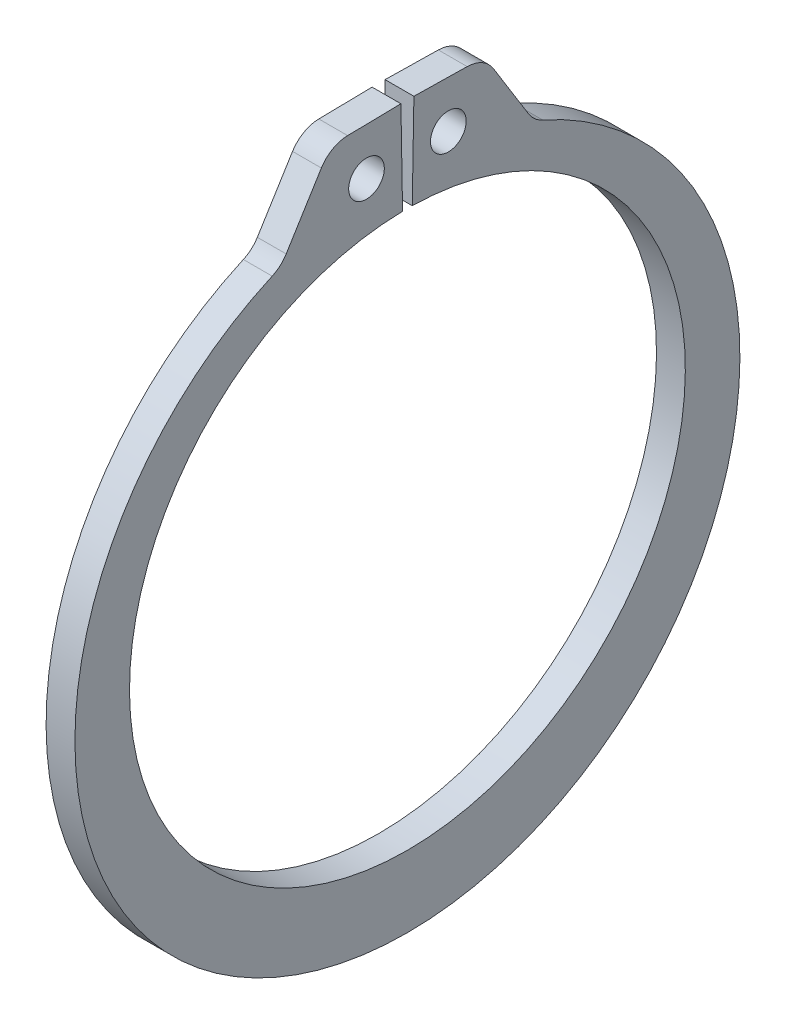
SolidWorks part; units mm, degrees
material "Cast Carbon Steel"
ref_plane "Front" through (0, 0, 0) normal (0, 0, 1) x (1, 0, 0)
ref_plane "Top" through (0, 0, 0) normal (0, 1, 0) x (1, 0, 0)
ref_plane "Right" through (0, 0, 0) normal (1, 0, 0) x (0, 0, -1)
sketch "Sketch1" plane through (0, 0, 0) normal (1, 0, 0) x (0, 0, -1)
  line L0 (0, 0) -> (0, 10.287) construction
  line L1 (-0.1795, 10.2854) -> (-0.2403, 13.7647)
  line L2 (0.2403, 13.7647) -> (2.8497, 13.7192)
  line L3 (2.8497, 13.7192) -> (4.6815, 10.7605)
  line L4 (0.1795, 10.2854) -> (0.2403, 13.7647)
  line L5 (-0.2403, 13.7647) -> (-2.8497, 13.7192)
  line L6 (-2.8497, 13.7192) -> (-4.6815, 10.7605)
  line L7 (-4.6815, 10.7605) -> (-4.1039, 9.4329) construction
  line L8 (4.6815, 10.7605) -> (4.1039, 9.4329) construction
  line L9 (0, -10.287) -> (0, -12.9286) construction
  line L10 (-2.8497, 13.7192) -> (-0.1795, 10.2854) construction
  line L11 (0, 10.287) -> (0, 13.7668) construction
  line L12 (-10.287, 0) -> (10.287, 0) construction
  circle A0 centre (0, 0) radius 10.287 construction
  arc A1 (-0.1795, 10.2854) -> (0.1795, 10.2854) centre (0, 0) ccw
  circle A3 centre (0, 0) radius 15.0495 construction
  circle A4 centre (-1.5146, 12.0023) radius 0.6604
  circle A5 centre (1.5146, 12.0023) radius 0.6604
  arc A6 (-4.6815, 10.7605) -> (4.6815, 10.7605) centre (0, -0.6214) ccw
  point P0 (0, -12.9286)
  dimension "A" = 20.574
  dimension "Hole" = 1.3208
  dimension "Smin" = 1.4478
  dimension "H" = 3.4798
  dimension "D2" = 2.6098
  dimension "Angle" = 1
extrude "Extrude1" add sketch "Sketch1" along normal mid plane 1.0668
fillet "Fillet1" radius 1.1684 4 edges at (0, 10.7605, 4.6815) (0, 10.7605, -4.6815) (0, 13.7192, 2.8497) (0, 13.7192, -2.8497)
sketch "Sketch2" plane through (0, 0, 0) normal (0, 0, 1) x (1, 0, 0)
  line L0 (-5.9182, 0) -> (15.4178, 0)
  line L1 (15.4178, 0) -> (15.4178, -11.1125)
  line L2 (-0.5842, -11.1125) -> (-5.2324, -11.1125)
  line L3 (15.4178, -11.1125) -> (0.5842, -11.1125)
  line L4 (0.5842, -11.1125) -> (0.5842, -10.4267)
  line L5 (0.5842, -10.4267) -> (-0.5842, -10.4267)
  line L6 (-0.5842, -10.4267) -> (-0.5842, -11.1125)
  line L7 (-0.5842, -11.1125) -> (-5.9182, -11.1125) construction
  line L8 (-5.9182, -11.1125) -> (-5.9182, 0) construction
  line L9 (15.4178, 0) -> (76.391, 0) construction
  line L10 (-5.2324, -11.1125) -> (-5.9182, -10.4267)
  line L11 (-5.9182, -10.4267) -> (-5.9182, 0)
  point P10 (0, -10.4267)
  dimension "D2" = 21.336
  dimension "D3" = 5.334
  dimension "D1" = 45
revolve "Revolve1" [suppressed] add sketch "Sketch2" angle 360 about L9
delete or keep bodies "Body-Delete1" [suppressed] type delete bodies bodies 122
equation "\"D2@Sketch2\" = \"D1@Extrude1\"*20"
equation "\"D3@Sketch2\" = \"D2@Sketch2\"/4"
equation "\"D2@Sketch1\" = \"H@Sketch1\"*.75"
